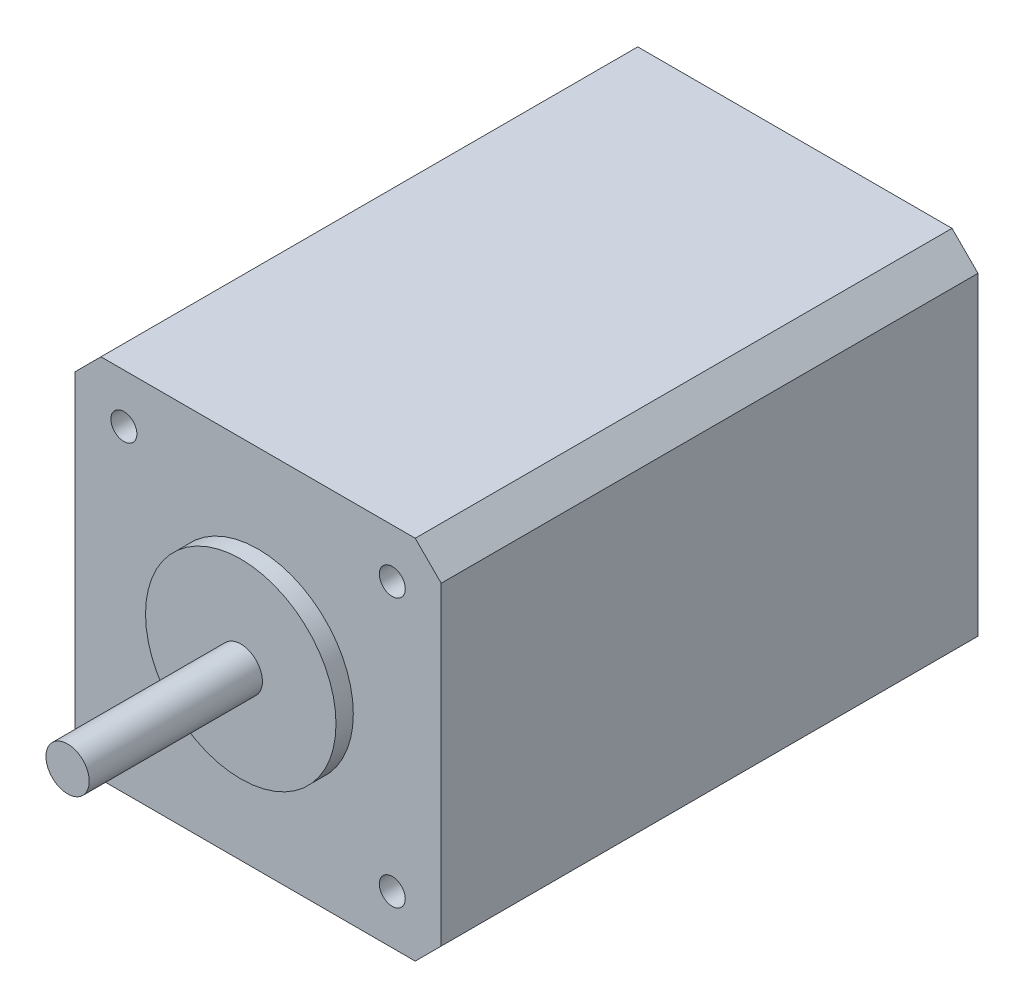
SolidWorks part; units mm, degrees
ref_plane "前视基准面" through (0, 0, 0) normal (0, 0, 1) x (1, 0, 0)
ref_plane "上视基准面" through (0, 0, 0) normal (0, 1, 0) x (1, 0, 0)
ref_plane "右视基准面" through (0, 0, 0) normal (1, 0, 0) x (0, 0, -1)
sketch "草图1" plane through (0, 0, 0) normal (0, 0, 1) x (1, 0, 0)
  line L1 (-21.15, 21.15) -> (21.15, 21.15)
  line L2 (-21.15, 21.15) -> (-21.15, -21.15)
  line L3 (-21.15, -21.15) -> (21.15, -21.15)
  line L4 (21.15, 21.15) -> (21.15, -21.15)
  line L5 (-21.15, 21.15) -> (21.15, -21.15) construction
  line L6 (-21.15, -21.15) -> (21.15, 21.15) construction
  point P0 (0, 0)
  dimension "D1" = 42.3
extrude "凸台-拉伸1" add sketch "草图1" along normal blind 62
sketch "草图2" plane through (0, 0, 62) normal (0, 0, 1) x (1, 0, 0)
  circle A0 centre (0, 0) radius 11
  dimension "D1" = 22
extrude "凸台-拉伸2" add sketch "草图2" along normal blind 2
sketch "草图3" plane through (0, 0, 64) normal (0, 0, 1) x (1, 0, 0)
  circle A0 centre (0, 0) radius 2.5
  dimension "D1" = 5
extrude "凸台-拉伸3" add sketch "草图3" along normal blind 20
chamfer "倒角1" distance 3 angle 45 4 edges at (21.15, 21.15, 31) (-21.15, 21.15, 31) (21.15, -21.15, 31) (-21.15, -21.15, 31)
sketch "草图4" plane through (0, 0, 62) normal (0, 0, 1) x (1, 0, 0)
  line L1 (15.5, -15.5) -> (-15.5, -15.5) construction
  line L2 (15.5, -15.5) -> (15.5, 15.5) construction
  line L3 (15.5, 15.5) -> (-15.5, 15.5) construction
  line L4 (-15.5, -15.5) -> (-15.5, 15.5) construction
  line L5 (15.5, -15.5) -> (-15.5, 15.5) construction
  line L6 (15.5, 15.5) -> (-15.5, -15.5) construction
  circle A0 centre (15.5, -15.5) radius 1.5
  circle A1 centre (-15.5, -15.5) radius 1.5
  circle A2 centre (15.5, 15.5) radius 1.5
  circle A3 centre (-15.5, 15.5) radius 1.5
  point P0 (0, 0)
  dimension "D2" = 3
  dimension "D1" = 31
extrude "切除-拉伸1" cut sketch "草图4" against normal blind 10
